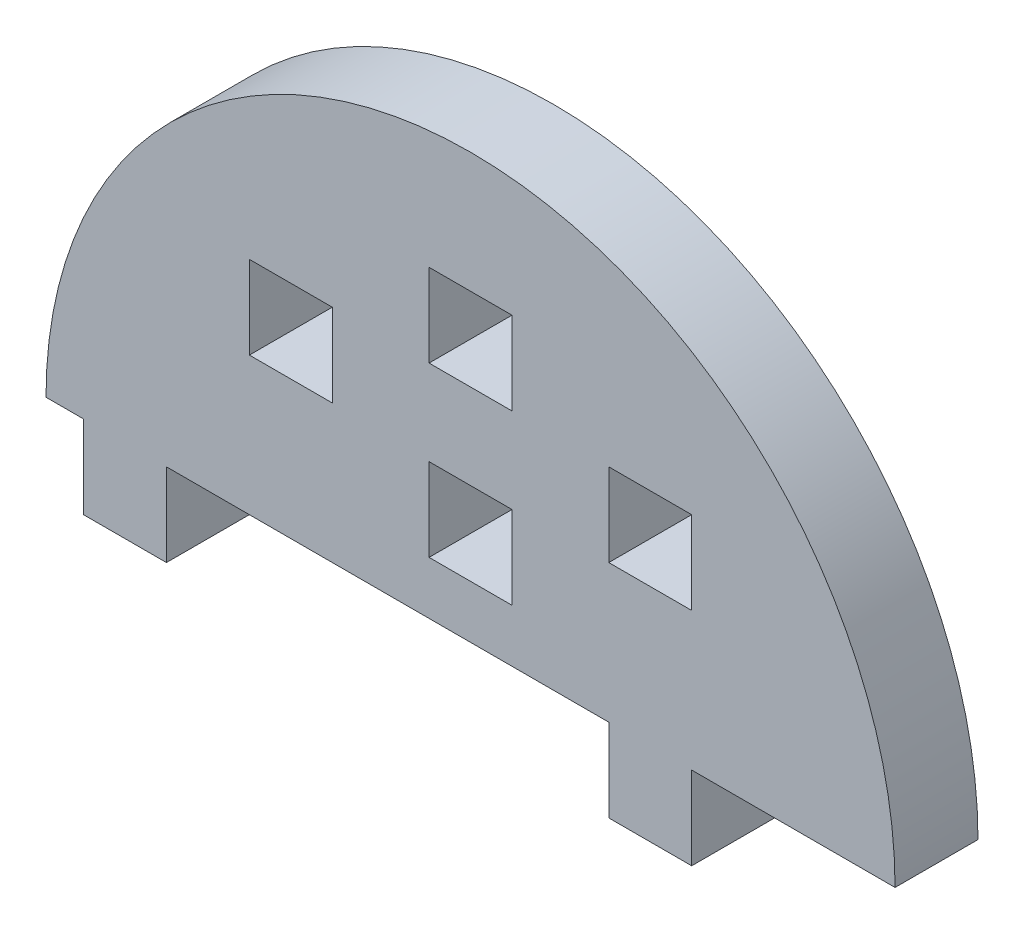
SolidWorks part; units mm, degrees
ref_plane "Front Plane" through (0, 0, 0) normal (0, 0, 1) x (1, 0, 0)
ref_plane "Top Plane" through (0, 0, 0) normal (0, 1, 0) x (1, 0, 0)
ref_plane "Right Plane" through (0, 0, 0) normal (1, 0, 0) x (0, 0, -1)
sketch "Model" plane through (0, 0, 0) normal (0, 0, 1) x (1, 0, 0)
  line L0 (3681.8003, 1334.9287) -> (3681.8003, 1328.9287)
  line L1 (3681.8003, 1328.9287) -> (3687.8003, 1328.9287)
  line L2 (3687.8003, 1328.9287) -> (3687.8003, 1334.9287)
  line L3 (3681.8003, 1350.9287) -> (3687.8003, 1350.9287)
  line L4 (3687.8003, 1350.9287) -> (3687.8003, 1344.9287)
  line L5 (3687.8003, 1344.9287) -> (3681.8003, 1344.9287)
  line L6 (3681.8003, 1344.9287) -> (3681.8003, 1350.9287)
  line L7 (3661.8003, 1350.9287) -> (3655.8003, 1350.9287)
  line L8 (3655.8003, 1350.9287) -> (3655.8003, 1344.9287)
  line L9 (3655.8003, 1344.9287) -> (3661.8003, 1344.9287)
  line L10 (3661.8003, 1344.9287) -> (3661.8003, 1350.9287)
  line L11 (3668.8003, 1356.9287) -> (3674.8003, 1356.9287)
  line L12 (3674.8003, 1356.9287) -> (3674.8003, 1350.9287)
  line L13 (3674.8003, 1350.9287) -> (3668.8003, 1350.9287)
  line L14 (3668.8003, 1350.9287) -> (3668.8003, 1356.9287)
  line L15 (3668.8003, 1338.7532) -> (3674.8003, 1338.7532)
  line L16 (3674.8003, 1338.7532) -> (3674.8003, 1344.7532)
  line L17 (3674.8003, 1344.7532) -> (3668.8003, 1344.7532)
  line L18 (3668.8003, 1344.7532) -> (3668.8003, 1338.7532)
  line L19 (3649.8003, 1334.9287) -> (3649.8003, 1328.9287)
  line L20 (3649.8003, 1328.9287) -> (3643.8003, 1328.9287)
  line L21 (3643.8003, 1328.9287) -> (3643.8003, 1334.9287)
  line L22 (3641.086, 1334.9287) -> (3643.8003, 1334.9287)
  line L23 (3649.8003, 1334.9287) -> (3681.8003, 1334.9287)
  line L24 (3687.8003, 1334.9287) -> (3702.5146, 1334.9287)
  arc A0 (3702.5146, 1334.9287) -> (3641.086, 1334.9287) centre (3671.8003, 1334.9287) ccw
extrude "Boss-Extrude1" add sketch "Model" along normal blind 6 contours L9 L10 L7 L8 | L14 L13 L12 L11 | L17 L18 L15 L16 | L6 L5 L4 L3 | A0 L22 L21 L20 L19 L23 L0 L1 L2 L24
